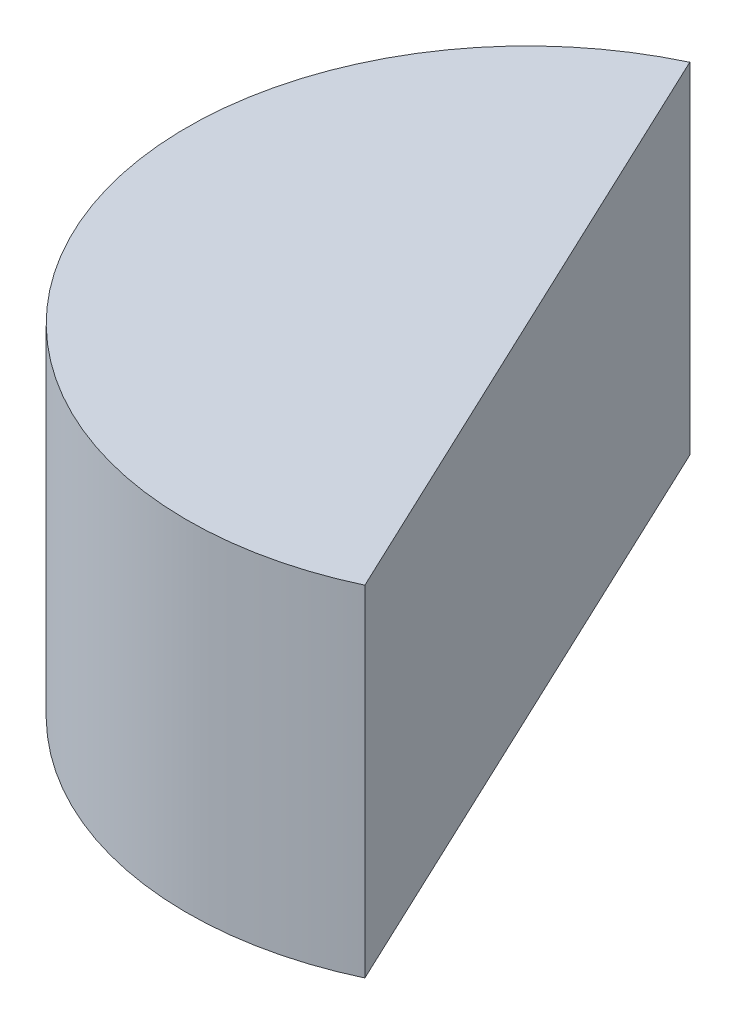
SolidWorks part; units mm, degrees
ref_plane "Front Plane" through (0, 0, 0) normal (0, 0, 1) x (1, 0, 0)
ref_plane "Top Plane" through (0, 0, 0) normal (0, 1, 0) x (1, 0, 0)
ref_plane "Right Plane" through (0, 0, 0) normal (1, 0, 0) x (0, 0, -1)
sketch "Sketch1" plane through (0, 0, 0) normal (0, 1, 0) x (1, 0, 0)
  line L0 (16.2621, -34.4551) -> (-16.2621, 34.4551)
  arc A0 (-16.2621, 34.4551) -> (16.2621, -34.4551) centre (0, 0) ccw
  point P6 (0, 0)
  dimension "D1" = 76.2
extrude "Boss-Extrude1" add sketch "Sketch1" along normal blind 38.1
